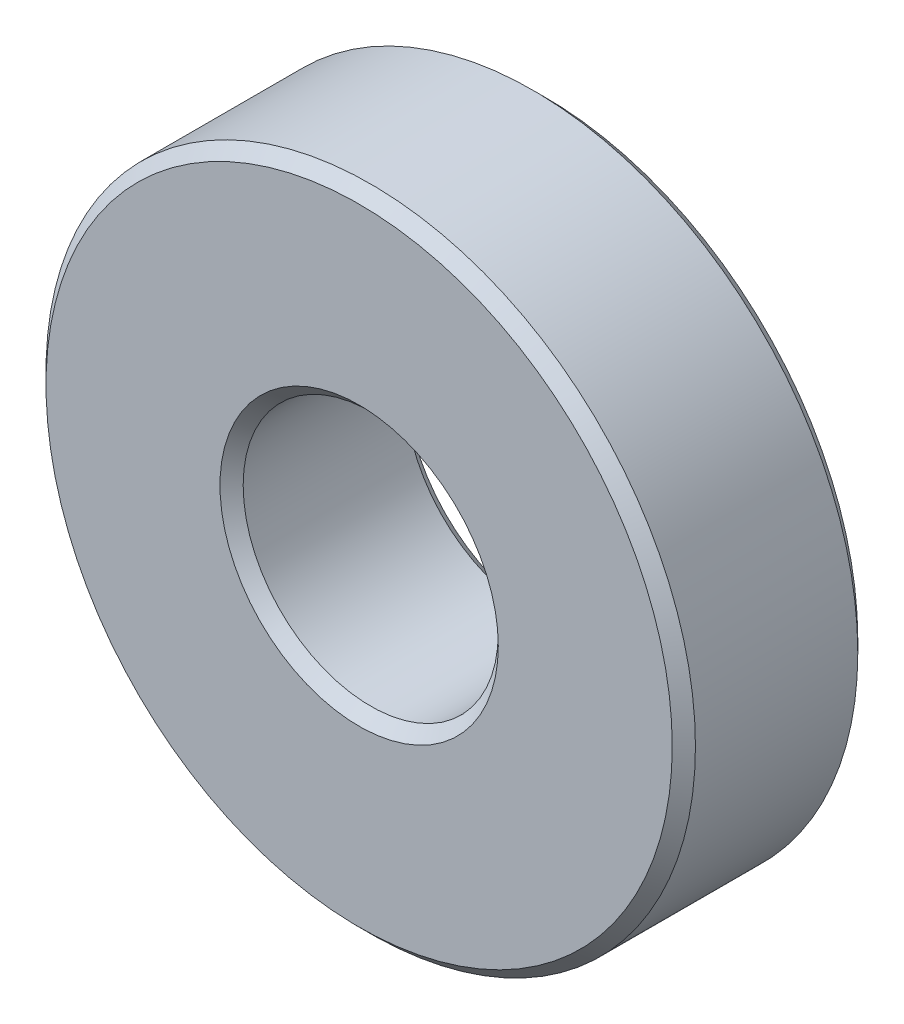
SolidWorks part; units mm, degrees
ref_plane "Front Plane (Z)" through (0, 0, 0) normal (0, 0, 1) x (1, 0, 0)
ref_plane "Top Plane (Y)" through (0, 0, 0) normal (0, 1, 0) x (1, 0, 0)
ref_plane "Side Plane (X)" through (0, 0, 0) normal (1, 0, 0) x (0, 0, -1)
sketch "Sketch1" plane through (0, 0, 0) normal (0, 0, 1) x (1, 0, 0)
  circle A0 centre (0, 0) radius 5.5
  circle A1 centre (0, 0) radius 14
  dimension "D1" = 11
  dimension "D2" = 28
extrude "Boss-Extrude1" add sketch "Sketch1" along normal blind 8
chamfer "Chamfer1" distance 0.5 angle 45 4 edges at (5.5, 0, 0) (14, 0, 0) (5.5, 0, 8) (14, 0, 8)
